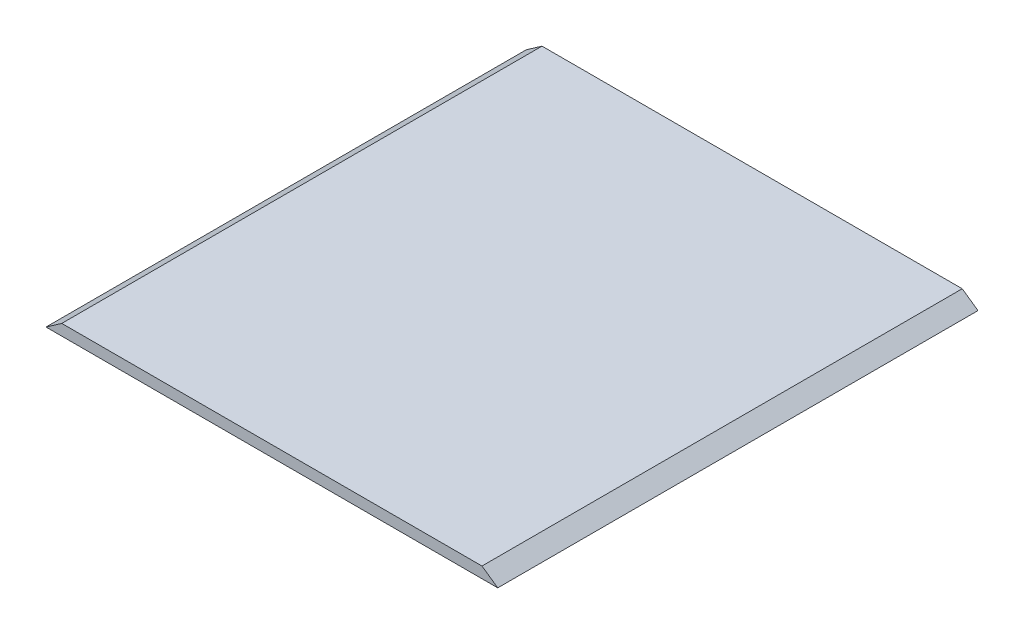
SolidWorks part; units mm, degrees
material "ABS"
ref_plane "Plano frontal" through (0, 0, 0) normal (0, 0, 1) x (1, 0, 0)
ref_plane "Plano superior" through (0, 0, 0) normal (0, 1, 0) x (1, 0, 0)
ref_plane "Plano direito" through (0, 0, 0) normal (1, 0, 0) x (0, 0, -1)
sketch "Esboço1" plane through (0, 0, 0) normal (0, 0, 1) x (1, 0, 0)
  line L0 (-87.5, -2.3) -> (-94.0695, -2.3)
  line L1 (87.5, -2.3) -> (-87.5, -2.3)
  line L2 (87.5, -2.3) -> (87.5, 2.3)
  line L3 (87.5, 2.3) -> (-87.5, 2.3)
  line L4 (-87.5, -2.3) -> (-87.5, 2.3)
  line L5 (87.5, -2.3) -> (-87.5, 2.3) construction
  line L6 (87.5, 2.3) -> (-87.5, -2.3) construction
  line L7 (-87.5, 2.3) -> (-94.0695, -2.3)
  line L8 (0, 11.1752) -> (0, -13.4378) construction
  line L9 (87.5, 2.3) -> (94.0695, -2.3)
  line L10 (87.5, -2.3) -> (87.5, 2.3)
  line L11 (87.5, -2.3) -> (94.0695, -2.3)
  point P0 (0, 0)
  dimension "D1" = 4.6
  dimension "D2" = 175
  dimension "D3" = 55
extrude "Ressalto-extrusão1" add sketch "Esboço1" along normal blind 200 contours L4 L7 L0 | L4 L1 L2 L3 | L2 L11 L9
